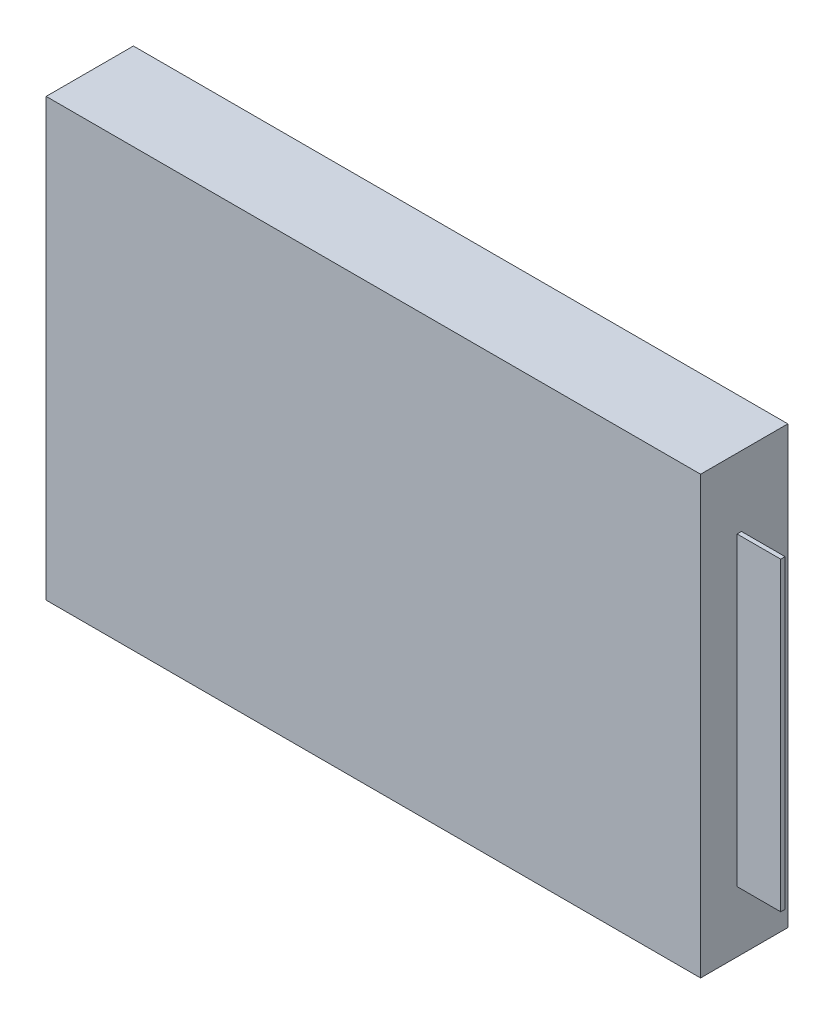
SolidWorks part; units mm, degrees
ref_plane "Front Plane" through (0, 0, 0) normal (0, 0, 1) x (1, 0, 0)
ref_plane "Top Plane" through (0, 0, 0) normal (0, 1, 0) x (1, 0, 0)
ref_plane "Right Plane" through (0, 0, 0) normal (1, 0, 0) x (0, 0, -1)
sketch "Sketch1" plane through (0, 0, 0) normal (0, 0, 1) x (1, 0, 0)
  line L1 (-15, -10) -> (15, -10)
  line L2 (-15, -10) -> (-15, 10)
  line L3 (-15, 10) -> (15, 10)
  line L4 (15, -10) -> (15, 10)
  line L5 (-15, -10) -> (15, 10) construction
  line L6 (-15, 10) -> (15, -10) construction
  point P0 (0, 0)
  dimension "D1" = 30
  dimension "D2" = 20
extrude "Boss-Extrude2" add sketch "Sketch1" along normal blind 4
sketch "Sketch2" plane through (15, 0, 0) normal (1, 0, 0) x (0, 0, -1)
  line L5 (-2.3254, -7.2099) -> (-2.1254, -7.2099)
  line L6 (-2.3254, -7.2099) -> (-2.3254, 6.7901)
  line L7 (-2.3254, 6.7901) -> (-2.1254, 6.7901)
  line L8 (-2.1254, -7.2099) -> (-2.1254, 6.7901)
  line L9 (-2.3254, -7.2099) -> (-2.1254, 6.7901) construction
  line L10 (-2.3254, 6.7901) -> (-2.1254, -7.2099) construction
  point P4 (-2.2254, -0.2099)
  dimension "D1" = 0.2
  dimension "D2" = 14
extrude "Boss-Extrude4" add sketch "Sketch2" along normal blind 2 contours L6 L7 L8 L5
